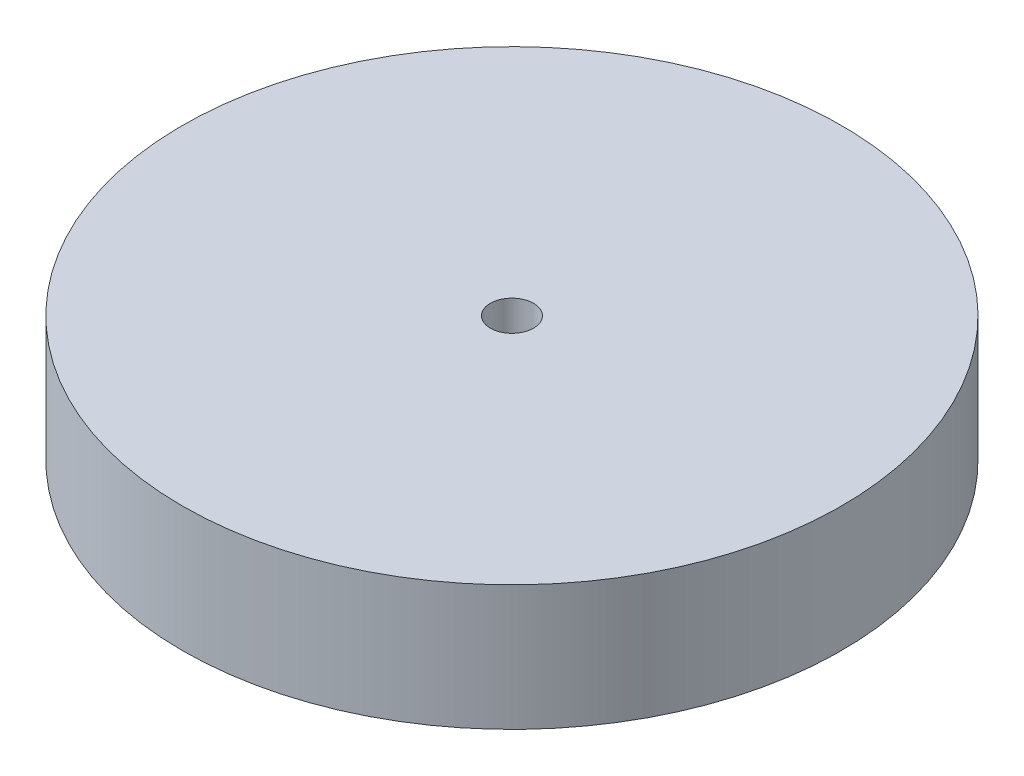
SolidWorks part; units mm, degrees
ref_plane "Front Plane" through (0, 0, 0) normal (0, 0, 1) x (1, 0, 0)
ref_plane "Top Plane" through (0, 0, 0) normal (0, 1, 0) x (1, 0, 0)
ref_plane "Right Plane" through (0, 0, 0) normal (1, 0, 0) x (0, 0, -1)
sketch "Sketch1" plane through (0, 0, 0) normal (0, 1, 0) x (1, 0, 0)
  circle A0 centre (0, 0) radius 50
  dimension "D1" = 100
extrude "Boss-Extrude1" add sketch "Sketch1" along normal blind 19
sketch "Sketch2" plane through (0, 19, 0) normal (0, 1, 0) x (1, 0, 0)
  circle A0 centre (0, 0) radius 3.275
  dimension "D1" = 6.55
extrude "Cut-Extrude2" cut sketch "Sketch2" against normal through all
